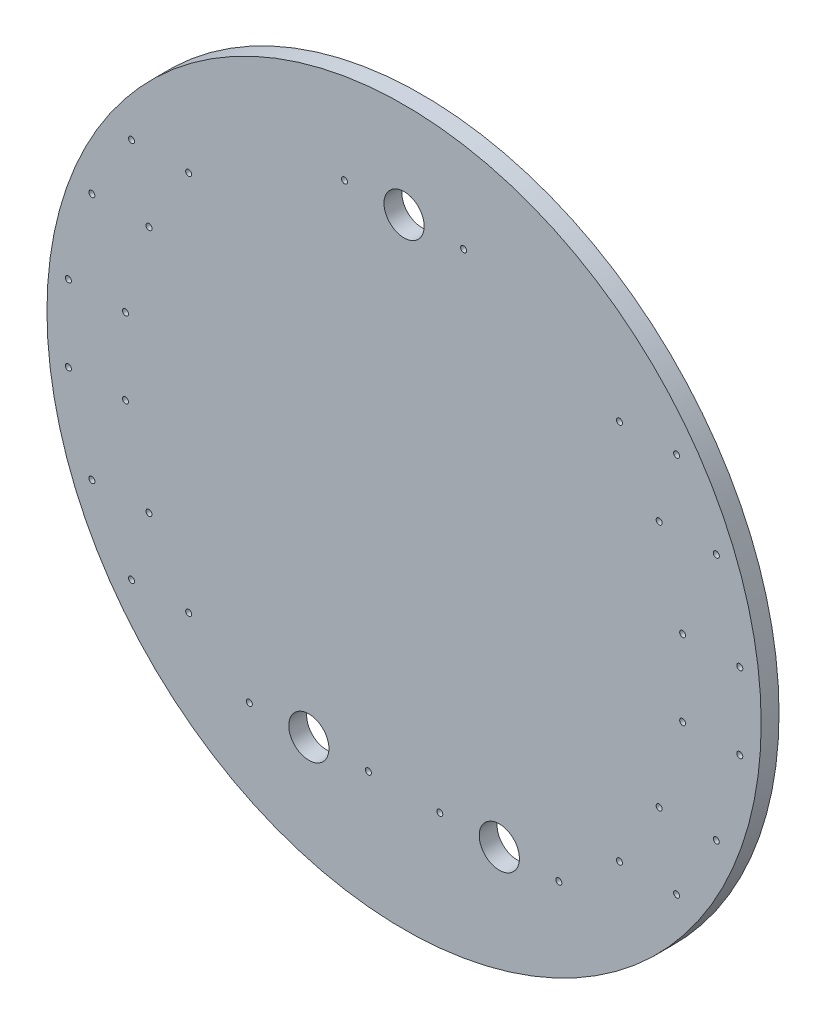
SolidWorks part; units mm, degrees
material "Delrin 2700 NC010, Low Viscosity Acetal Copolymer (SS)"
ref_plane "Front Plane" through (0, 0, 0) normal (0, 0, 1) x (1, 0, 0)
ref_plane "Top Plane" through (0, 0, 0) normal (0, 1, 0) x (1, 0, 0)
ref_plane "Right Plane" through (0, 0, 0) normal (1, 0, 0) x (0, 0, -1)
sketch "Sketch1" plane through (0, 0, 0) normal (0, 0, 1) x (1, 0, 0)
  circle A0 centre (0, 0) radius 95.25
  dimension "D1" = 190.5
extrude "Boss-Extrude1" add sketch "Sketch1" along normal blind 4.7625
hole_wizard "M2x0.4 Tapped Hole1" positions "Sketch3" profile "Sketch2" tap size "M2x0.4" standard "ANSI Metric"
sketch "Sketch3" plane through (0, 0, 4.7625) normal (0, 0, 1) x (1, 0, 0)
  line L0 (-83.2783, 33.02) -> (-68.0383, 33.02) construction
  line L1 (0, 0) -> (-124.3525, 0) construction
  line L2 (-72.6881, 50.8) -> (-57.4481, 50.8) construction
  line L3 (-89.5424, 10.16) -> (-74.3024, 10.16) construction
  line L5 (-72.6881, -50.8) -> (-57.4481, -50.8) construction
  line L6 (-83.2783, -33.02) -> (-68.0383, -33.02) construction
  line L7 (-89.5424, -10.16) -> (-74.3024, -10.16) construction
  line L8 (0, 0) -> (0, 116.1082) construction
  line L10 (72.6881, -50.8) -> (57.4481, -50.8) construction
  line L11 (83.2783, -33.02) -> (68.0383, -33.02) construction
  line L12 (89.5424, -10.16) -> (74.3024, -10.16) construction
  line L13 (89.5424, 10.16) -> (74.3024, 10.16) construction
  line L14 (83.2783, 33.02) -> (68.0383, 33.02) construction
  line L15 (72.6881, 50.8) -> (57.4481, 50.8) construction
  circle A0 centre (0, 0) radius 82.55 construction
  point P0 (-83.2783, 33.02)
  point P2 (-68.0383, 33.02)
  point P19 (-75.6583, 33.02)
  point P25 (-72.6881, 50.8)
  point P27 (-57.4481, 50.8)
  point P34 (-65.0681, 50.8)
  point P35 (-89.5424, 10.16)
  point P37 (-74.3024, 10.16)
  point P44 (-81.9224, 10.16)
  point P45 (-57.4481, -50.8)
  point P46 (-72.6881, -50.8)
  point P48 (-68.0383, -33.02)
  point P49 (-83.2783, -33.02)
  point P51 (-74.3024, -10.16)
  point P52 (-89.5424, -10.16)
  point P60 (57.4481, -50.8)
  point P61 (72.6881, -50.8)
  point P64 (68.0383, -33.02)
  point P65 (83.2783, -33.02)
  point P68 (89.5424, -10.16)
  point P70 (74.3024, -10.16)
  point P71 (89.5424, 10.16)
  point P73 (74.3024, 10.16)
  point P74 (83.2783, 33.02)
  point P76 (68.0383, 33.02)
  point P77 (57.4481, 50.8)
  point P78 (72.6881, 50.8)
  dimension "D4" = 165.1
  dimension "D1" = 15.24
  dimension "D2" = 33.02
  dimension "D3" = 15.24
  dimension "D5" = 50.8
  dimension "D6" = 15.24
  dimension "D7" = 10.16
sketch "Sketch2" plane through (-83.2783, 33.02, 4.7625) normal (1, 0, 0) x (0, -1, 0)
  line L0 (0, 0) -> (0, 5.334)
  line L1 (0, 5.334) -> (0.8, 5.334)
  line L2 (0.8, 5.334) -> (0.8, 0)
  line L5 (0.8, 0) -> (0, 0)
  line L10 (0, 5.334) -> (-0.8, 5.334) construction
  line L11 (0, -6.35) -> (0, 107.95) construction
  dimension "Tap Drill Dia." = 1.6
  dimension "Tap Drill Depth" = 5.334
  dimension "Drill Angle" = 180
cosmetic thread "Hole Thread1" parameters "D1"=4.064, "D2"=2
cosmetic thread "Hole Thread2" parameters "D1"=4.064, "D2"=2
cosmetic thread "Hole Thread3" parameters "D1"=4.064, "D2"=2
cosmetic thread "Hole Thread4" parameters "D1"=4.064, "D2"=2
cosmetic thread "Hole Thread5" parameters "D1"=4.064, "D2"=2
cosmetic thread "Hole Thread6" parameters "D1"=4.064, "D2"=2
cosmetic thread "Hole Thread7" parameters "D1"=4.064, "D2"=2
cosmetic thread "Hole Thread8" parameters "D1"=4.064, "D2"=2
cosmetic thread "Hole Thread9" parameters "D1"=4.064, "D2"=2
cosmetic thread "Hole Thread10" parameters "D1"=4.064, "D2"=2
cosmetic thread "Hole Thread11" parameters "D1"=4.064, "D2"=2
cosmetic thread "Hole Thread12" parameters "D1"=4.064, "D2"=2
cosmetic thread "Hole Thread13" parameters "D1"=4.064, "D2"=2
cosmetic thread "Hole Thread14" parameters "D1"=4.064, "D2"=2
cosmetic thread "Hole Thread15" parameters "D1"=4.064, "D2"=2
cosmetic thread "Hole Thread16" parameters "D1"=4.064, "D2"=2
cosmetic thread "Hole Thread17" parameters "D1"=4.064, "D2"=2
cosmetic thread "Hole Thread18" parameters "D1"=4.064, "D2"=2
cosmetic thread "Hole Thread19" parameters "D1"=4.064, "D2"=2
cosmetic thread "Hole Thread20" parameters "D1"=4.064, "D2"=2
cosmetic thread "Hole Thread21" parameters "D1"=4.064, "D2"=2
cosmetic thread "Hole Thread22" parameters "D1"=4.064, "D2"=2
cosmetic thread "Hole Thread23" parameters "D1"=4.064, "D2"=2
cosmetic thread "Hole Thread24" parameters "D1"=4.064, "D2"=2
hole_wizard "M2x0.4 Tapped Hole2" positions "Sketch5" profile "Sketch4" tap size "M2x0.4" standard "ANSI Metric"
sketch "Sketch5" plane through (0, 0, 4.7625) normal (0, 0, 1) x (1, 0, 0)
  line L0 (-41.275, -63.5) -> (-9.525, -63.5) construction
  line L2 (0, 0) -> (0, -53.0091) construction
  line L3 (-15.875, 69.85) -> (15.875, 69.85) construction
  line L4 (-25.4, -63.5) -> (-25.4, -33.7261) construction
  point P0 (-41.275, -63.5)
  point P2 (-9.525, -63.5)
  point P14 (9.525, -63.5)
  point P15 (41.275, -63.5)
  point P16 (-15.875, 69.85)
  point P18 (15.875, 69.85)
  point P26 (0, 69.85)
  dimension "D1" = 31.75
  dimension "D2" = 63.5
  dimension "D3" = 25.4
  dimension "D4" = 31.75
  dimension "D5" = 69.85
sketch "Sketch4" plane through (-41.275, -63.5, 4.7625) normal (1, 0, 0) x (0, -1, 0)
  line L0 (0, 0) -> (0, 5.334)
  line L1 (0, 5.334) -> (0.8, 5.334)
  line L2 (0.8, 5.334) -> (0.8, 0)
  line L5 (0.8, 0) -> (0, 0)
  line L10 (0, 5.334) -> (-0.8, 5.334) construction
  line L11 (0, -6.35) -> (0, 107.95) construction
  dimension "Tap Drill Dia." = 1.6
  dimension "Tap Drill Depth" = 5.334
  dimension "Drill Angle" = 180
cosmetic thread "Hole Thread25" parameters "D1"=4.064, "D2"=2
cosmetic thread "Hole Thread26" parameters "D1"=4.064, "D2"=2
cosmetic thread "Hole Thread27" parameters "D1"=4.064, "D2"=2
cosmetic thread "Hole Thread28" parameters "D1"=4.064, "D2"=2
cosmetic thread "Hole Thread29" parameters "D1"=4.064, "D2"=2
cosmetic thread "Hole Thread30" parameters "D1"=4.064, "D2"=2
hole_wizard "1/2-13 Tapped Hole1" positions "Sketch10" profile "Sketch9" tap size "1/2-13" standard "ANSI Inch"
sketch "Sketch10" plane through (0, 0, 4.7625) normal (0, 0, 1) x (1, 0, 0)
  line L0 (-15.875, 69.85) -> (15.875, 69.85) construction
  line L2 (-41.275, -63.5) -> (-9.525, -63.5) construction
  line L4 (9.525, -63.5) -> (41.275, -63.5) construction
  point P0 (0, 69.85)
  point P2 (-25.4, -63.5)
  point P4 (25.4, -63.5)
  point P12 (0, 69.85)
  point P19 (-25.4, -63.5)
  point P26 (25.4, -63.5)
sketch "Sketch9" plane through (0, 69.85, 4.7625) normal (1, 0, 0) x (0, -1, 0)
  line L0 (0, 0) -> (0, 31.242)
  line L1 (0, 31.242) -> (5.3581, 31.242)
  line L2 (5.3581, 31.242) -> (5.3581, 0)
  line L5 (5.3581, 0) -> (0, 0)
  line L10 (0, 31.242) -> (-5.3581, 31.242) construction
  line L11 (0, -6.35) -> (0, 107.95) construction
  dimension "Tap Drill Dia." = 10.7163
  dimension "Tap Drill Depth" = 31.242
  dimension "Drill Angle" = 180
cosmetic thread "Hole Thread35" parameters "D1"=4.7625, "D2"=12.7
cosmetic thread "Hole Thread36" parameters "D1"=4.7625, "D2"=12.7
cosmetic thread "Hole Thread37" parameters "D1"=4.7625, "D2"=12.7
